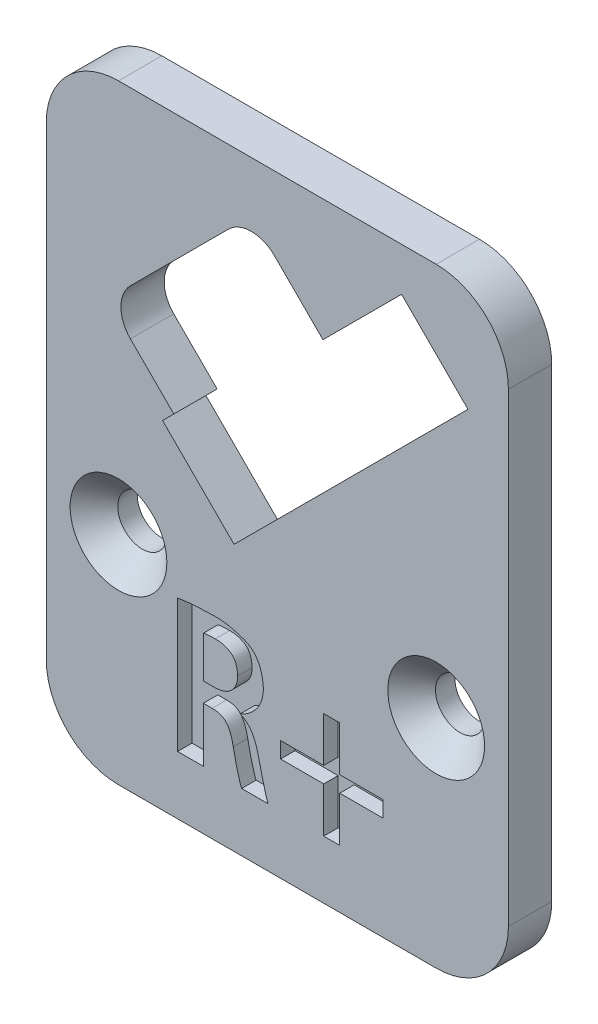
SolidWorks part; units mm, degrees
ref_plane "Front Plane" through (0, 0, 0) normal (0, 0, 1) x (1, 0, 0)
ref_plane "Top Plane" through (0, 0, 0) normal (0, 1, 0) x (1, 0, 0)
ref_plane "Right Plane" through (0, 0, 0) normal (1, 0, 0) x (0, 0, -1)
sketch "Sketch2" plane through (0, 0, 0) normal (0, 0, 1) x (1, 0, 0)
  line L0 (-43.3456, 10.9062) -> (-37.9009, 16.3509) construction
  line L1 (-46.8812, 14.4417) -> (-42.9921, 10.5526) construction
  line L2 (-33.6583, 12.1082) -> (-37.9009, 16.3509) construction
  line L3 (-40.6586, 5.1079) -> (-33.6583, 12.1082) construction
  line L4 (-40.6586, 5.1079) -> (-47.8711, -2.1046) construction
  line L5 (-49.4975, -3.731) -> (-47.8711, -2.1046) construction
  line L6 (-49.4975, -3.731) -> (-53.7401, 0.5117) construction
  line L8 (-52.6087, 0.936) -> (-56.4978, 4.825) construction
  line L9 (-56.4978, 7.6535) -> (-49.7096, 14.4417) construction
  line L10 (-43.3456, 10.9062) -> (-37.9009, 16.3509) construction
  line L11 (-46.8812, 14.4417) -> (-42.9921, 10.5526) construction
  line L12 (-33.6583, 12.1082) -> (-37.9009, 16.3509) construction
  line L13 (-40.6586, 5.1079) -> (-33.6583, 12.1082) construction
  line L14 (-40.6586, 5.1079) -> (-47.8711, -2.1046) construction
  line L15 (-49.4975, -3.731) -> (-47.8711, -2.1046) construction
  line L16 (-49.4975, -3.731) -> (-53.7401, 0.5117) construction
  line L17 (-53.3159, 1.6431) -> (-54.0937, 0.8652) construction
  line L18 (-52.6087, 0.936) -> (-56.4978, 4.825) construction
  line L19 (-56.4978, 7.6535) -> (-49.7096, 14.4417) construction
  line L20 (-43.3456, 11.2597) -> (-37.9009, 16.7044)
  line L21 (-33.3047, 12.1082) -> (-37.9009, 16.7044)
  line L22 (-40.4819, 4.9311) -> (-33.3047, 12.1082)
  line L23 (-40.4819, 4.9311) -> (-47.6944, -2.2814)
  line L24 (-49.4975, -4.0845) -> (-47.6944, -2.2814)
  line L25 (-49.4975, -4.0845) -> (-54.2704, 0.6885)
  line L27 (-53.6694, 1.6431) -> (-56.6746, 4.6483)
  line L28 (-56.6746, 7.8302) -> (-49.8864, 14.6185)
  line L29 (-46.7044, 14.6185) -> (-43.3456, 11.2597)
  line L30 (-52.7855, 0.7592) -> (-56.6746, 4.6483) construction
  line L31 (-54.2704, 0.6885) -> (-52.8955, 0.8849) construction
  line L32 (-46.7044, 14.6185) -> (-42.8153, 10.7294) construction
  line L33 (-43.5224, 11.0829) -> (-37.9009, 16.7044) construction
  line L34 (-62.5, 22.5) -> (-62.5, -22.5) construction
  line L35 (-30.5047, 19.7044) -> (-62.5, 19.7044)
  line L36 (-30.5047, 19.7044) -> (-30.5047, -22.5)
  line L37 (-30.5047, -22.5) -> (-62.5, -22.5)
  line L38 (-62.5, 19.7044) -> (-62.5, -22.5)
  line L39 (-30.5047, 19.7044) -> (-62.5, -22.5) construction
  line L40 (-30.5047, -22.5) -> (-62.5, 19.7044) construction
  line L41 (-62.5, -22.5) -> (62.5, -22.5) construction
  line L43 (-53.7401, 0.5117) -> (-52.8602, 0.6374) construction
  line L44 (-53.4926, 1.4663) -> (-54.2704, 0.6885) construction
  line L45 (-53.6694, 1.6431) -> (-54.4472, 0.8652)
  line L46 (-54.4472, 0.8652) -> (-54.2704, 0.6885)
  arc A0 (-46.8812, 14.4417) -> (-49.7096, 14.4417) centre (-48.2954, 13.0275) ccw construction
  arc A1 (-56.4978, 7.6535) -> (-56.4978, 4.825) centre (-55.0836, 6.2393) ccw construction
  arc A2 (-46.8812, 14.4417) -> (-49.7096, 14.4417) centre (-48.2954, 13.0275) ccw construction
  arc A3 (-56.4978, 7.6535) -> (-56.4978, 4.825) centre (-55.0836, 6.2393) ccw construction
  arc A4 (-56.6746, 7.8302) -> (-56.6746, 4.6483) centre (-55.0836, 6.2393) ccw
  arc A5 (-46.7044, 14.6185) -> (-49.8864, 14.6185) centre (-48.2954, 13.0275) ccw
  point P5 (-46.5024, -1.3978)
  dimension "D2" = 3
  dimension "D3" = 2.8
  dimension "D4" = 0.25
  dimension "D1" = 0.25
extrude "Boss-Extrude2" add sketch "Sketch2" along normal blind 3
fillet "Fillet1" radius 5 4 edges at (-30.5047, -22.5, 1.5) (-62.5, -22.5, 1.5) (-62.5, 19.7044, 1.5) (-30.5047, 19.7044, 1.5)
sketch "Sketch3" plane through (0, 0, 3) normal (0, 0, 1) x (1, 0, 0)
  line L0 (-62.5, -18.5) -> (-30.5047, -18.5) construction
  line L1 (-62.5, 14.7044) -> (-62.5, -17.5) construction
  line L2 (-30.5047, -17.5) -> (-30.5047, 14.7044) construction
  line L3 (-57.5, -22.5) -> (-35.5047, -22.5) construction
  text T0 "R+" font "@Adobe Gothic Std B" height in points 30
  dimension "D1" = 4
extrude "Cut-Extrude1" cut sketch "Sketch3" against normal blind 1
sketch "Sketch4" plane through (0, 0, 3) normal (0, 0, 1) x (1, 0, 0)
  line L0 (-62.5, -7.5) -> (-30.5047, -7.5) construction
  line L1 (-62.5, 14.7044) -> (-62.5, -17.5) construction
  line L2 (-30.5047, -17.5) -> (-30.5047, 14.7044) construction
  line L3 (-57.5, -22.5) -> (-35.5047, -22.5) construction
  point P6 (-57.5, -7.5)
  point P7 (-35.5047, -7.5)
  dimension "D1" = 5
  dimension "D2" = 5
  dimension "D3" = 15
hole_wizard "CSK for M3 Countersunk Flat Head Screw1" positions "3DSketch1" profile "Sketch5" countersink size "M3" standard "DIN"
sketch3d "3DSketch1"
  point P0 (-57.5, -7.5, 3)
  point P3 (-35.5047, -7.5, 3)
sketch "Sketch5" plane through (-57.5, -7.5, 3) normal (1, 0, 0) x (0, -1, 0)
  line L0 (0, 0) -> (0, 21.0215)
  line L1 (0, 21.0215) -> (1.7, 20)
  line L2 (1.7, 20) -> (1.7, 1.65)
  line L3 (1.7, 1.65) -> (3.35, 0)
  line L5 (3.35, 0) -> (0, 0)
  line L6 (-1.7, 1.65) -> (-3.35, 0) construction
  line L10 (0, 21.0215) -> (-1.7, 20) construction
  line L11 (0, -6.35) -> (0, 107.95) construction
  dimension "Hole Dia." = 3.4
  dimension "Hole Depth" = 20
  dimension "Near C'Sink Dia." = 6.7
  dimension "Near C'Sink Angle" = 90
  dimension "Drill Angle" = 118
equation "\"D1@Sketch4\"=\"D2@Sketch4\""
